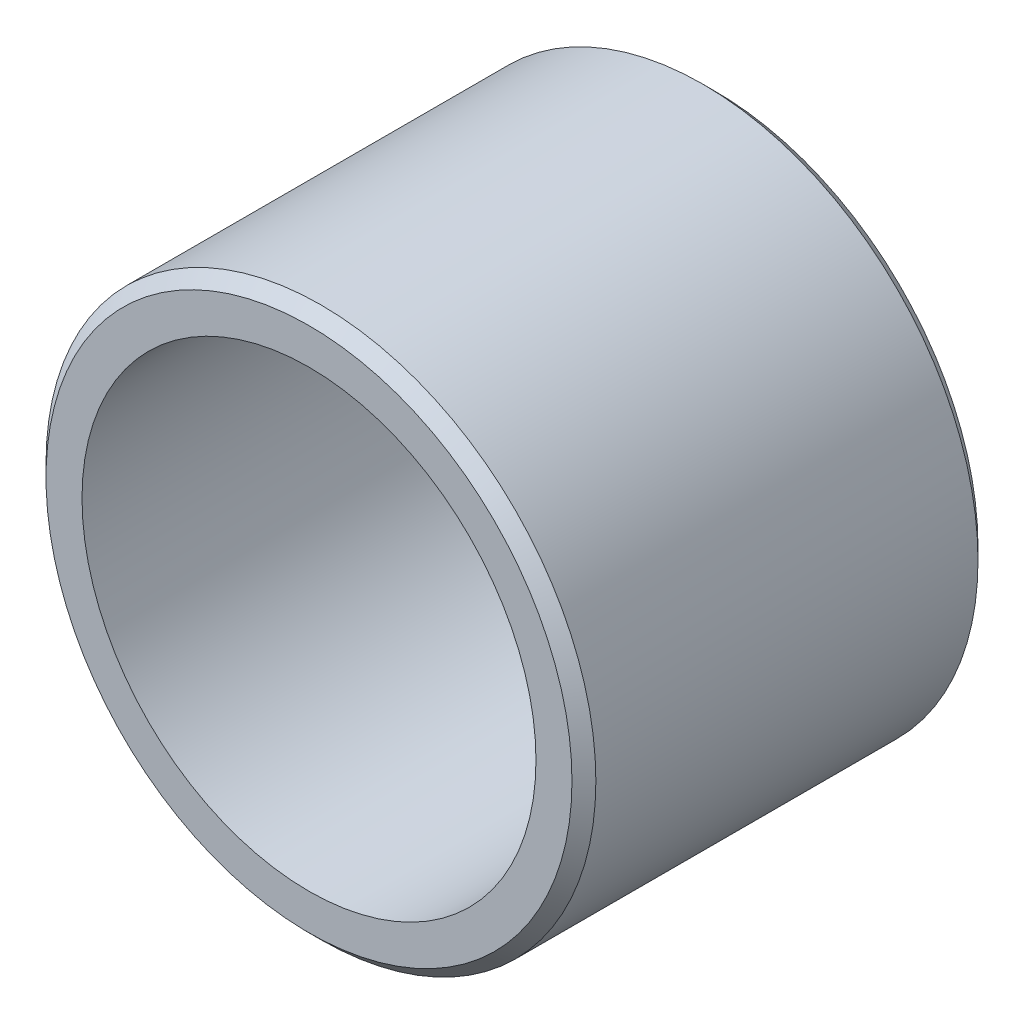
SolidWorks part; units mm, degrees
ref_plane "Front Plane" through (0, 0, 0) normal (0, 0, 1) x (1, 0, 0)
ref_plane "Top Plane" through (0, 0, 0) normal (0, 1, 0) x (1, 0, 0)
ref_plane "Right Plane" through (0, 0, 0) normal (1, 0, 0) x (0, 0, -1)
sketch "Sketch1" plane through (0, 0, 0) normal (0, 0, 1) x (1, 0, 0)
  circle A0 centre (0, 0) radius 9.4996
  circle A1 centre (0, 0) radius 11.5062
  dimension "D1" = 18.9992
  dimension "D2" = 23.0124
extrude "Boss-Extrude1" add sketch "Sketch1" against normal blind 16.9926
chamfer "Chamfer1" distance 0.5 angle 45 2 edges at (11.5062, 0, -16.9926) (11.5062, 0, 0)
